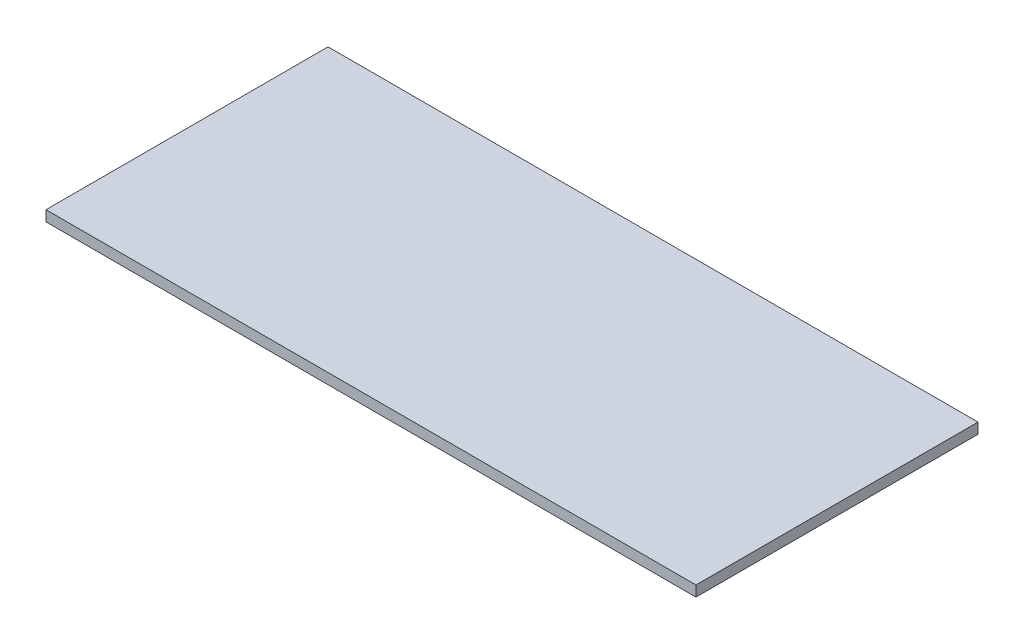
SolidWorks part; units mm, degrees
ref_plane "Front Plane" through (0, 0, 0) normal (0, 0, 1) x (1, 0, 0)
ref_plane "Top Plane" through (0, 0, 0) normal (0, 1, 0) x (1, 0, 0)
ref_plane "Right Plane" through (0, 0, 0) normal (1, 0, 0) x (0, 0, -1)
sketch "Sketch1" plane through (0, 0, 0) normal (0, 1, 0) x (1, 0, 0)
  line L1 (-51.5366, 22.3647) -> (51.5366, 22.3647)
  line L2 (-51.5366, 22.3647) -> (-51.5366, -22.3647)
  line L3 (-51.5366, -22.3647) -> (51.5366, -22.3647)
  line L4 (51.5366, 22.3647) -> (51.5366, -22.3647)
  line L5 (-51.5366, 22.3647) -> (51.5366, -22.3647) construction
  line L6 (-51.5366, -22.3647) -> (51.5366, 22.3647) construction
  point P0 (0, 0)
  dimension "D1" = 44.7294
  dimension "D2" = 103.0732
extrude "Boss-Extrude1" add sketch "Sketch1" along normal blind 1.6764
equation "\"controller_length\"=4.058"
equation "\"D2@Sketch1\"=\"controller_length\""
equation "\"controller_height\"=1.761"
equation "\"D1@Sketch1\"=\"controller_height\""
